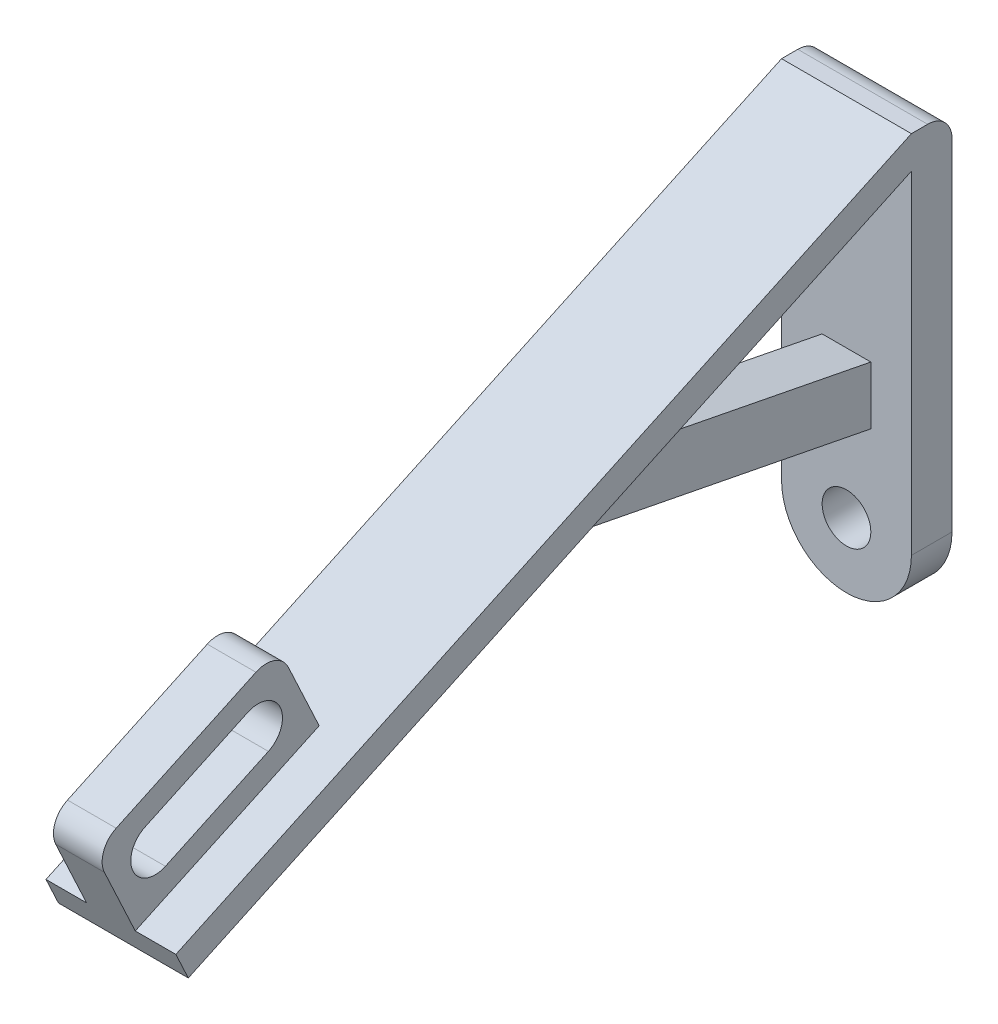
SolidWorks part; units mm, degrees
ref_plane "Alzado" through (0, 0, 0) normal (0, 0, 1) x (1, 0, 0)
ref_plane "Planta" through (0, 0, 0) normal (0, 1, 0) x (1, 0, 0)
ref_plane "Vista lateral" through (0, 0, 0) normal (1, 0, 0) x (0, 0, -1)
sketch "Croquis1" plane through (0, 0, 0) normal (0, 0, 1) x (1, 0, 0)
  line L0 (0, 0) -> (-8, 0) construction
  line L1 (-8, 0) -> (-8, 45)
  line L2 (0, 0) -> (0, 28.3464) construction
  line L3 (8, 0) -> (8, 45)
  line L4 (-8, 45) -> (8, 45)
  circle A0 centre (0, 0) radius 3
  arc A1 (-8, 0) -> (8, 0) centre (0, 0) ccw
  dimension "D1" = 6
  dimension "D2" = 8
  dimension "D3" = 45
extrude "Saliente-Extruir1" add sketch "Croquis1" along normal blind 5
sketch "Croquis2" plane through (-8, 0, 0) normal (-1, 0, 0) x (0, 0, 1)
  line L7 (5, 45) -> (95.6308, 2.7382)
  line L8 (95.6308, 2.7382) -> (94.0987, -0.5474)
  line L9 (94.0987, -0.5474) -> (5, 41)
  line L10 (5, 45) -> (5, 0) construction
  line L11 (5, 41) -> (5, 45)
  dimension "D1" = 4
  dimension "D2" = 65
  dimension "D3" = 100
extrude "Saliente-Extruir2" add sketch "Croquis2" against normal up to vertex (16 mm away)
ref_plane "Plano1" through (0, 0, 0) normal (1, 0, 0) x (0, 0, -1)
sketch "Croquis3" plane through (0, 0, 0) normal (1, 0, 0) x (0, 0, -1)
  line L0 (-5, 41) -> (-5, 11) construction
  line L1 (-5, 41) -> (-5, 0) construction
  line L2 (-5, 41) -> (-50.3154, 19.8691) construction
  line L3 (-5, 41) -> (-94.0987, -0.5474) construction
  line L4 (-5, 11) -> (-50.3154, 19.8691)
  line L5 (-5, 18.1328) -> (-39.5412, 24.8932)
  line L6 (-39.5412, 24.8932) -> (-50.3154, 19.8691)
  line L7 (-5, 18.1328) -> (-5, 11)
  dimension "D1" = 50
  dimension "D2" = 30
  dimension "D3" = 7
extrude "Saliente-Extruir3" add sketch "Croquis3" along normal blind 3 and the other way blind 3
sketch "Croquis4" plane through (0, 0, 0) normal (1, 0, 0) x (0, 0, -1)
  line L0 (-95.6308, 2.7382) -> (-100.7022, 13.6139)
  line L1 (-100.7022, 13.6139) -> (-78.0445, 24.1793)
  line L2 (-78.0445, 24.1793) -> (-72.9731, 13.3036)
  line L3 (-95.6308, 2.7382) -> (-5, 45) construction
  line L4 (-72.9731, 13.3036) -> (-95.6308, 2.7382)
  line L5 (-72.9731, 13.3036) -> (-100.7022, 13.6139) construction
  line L6 (-86.8376, 13.4587) -> (-93.1818, 10.5004) construction
  line L7 (-86.8376, 13.4587) -> (-80.4935, 16.4171) construction
  line L8 (-80.4935, 16.4171) -> (-93.1818, 10.5004) construction
  line L9 (-79.2256, 13.6982) -> (-91.9139, 7.7815)
  line L10 (-81.7613, 19.136) -> (-94.4497, 13.2193)
  arc A0 (-79.2256, 13.6982) -> (-81.7613, 19.136) centre (-80.4935, 16.4171) ccw
  arc A1 (-94.4497, 13.2193) -> (-91.9139, 7.7815) centre (-93.1818, 10.5004) ccw
  point P8 (-86.8376, 13.4587)
  dimension "D3" = 7
  dimension "D1" = 25
  dimension "D2" = 12
  dimension "D4" = 6
extrude "Saliente-Extruir4" add sketch "Croquis4" along normal blind 3 and the other way blind 3
fillet "Redondeo1" radius 3 3 edges at (0, 13.6139, 100.7022) (0, 24.1793, 78.0445) (0, 45, 0)
